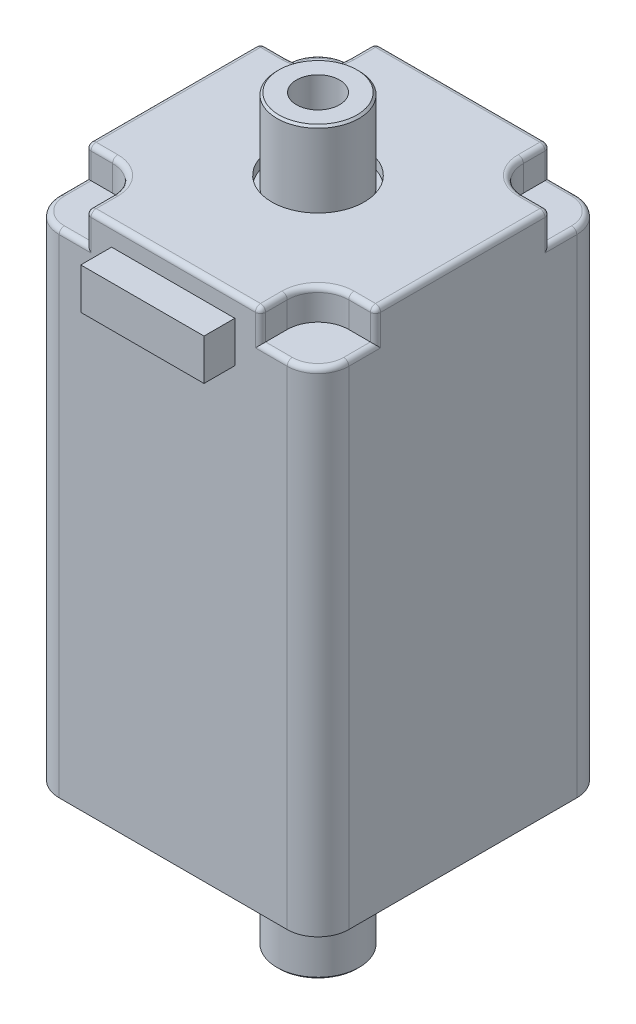
SolidWorks part; units mm, degrees
ref_plane "Front" through (0, 0, 0) normal (0, 0, 1) x (1, 0, 0)
ref_plane "Top" through (0, 0, 0) normal (0, 1, 0) x (1, 0, 0)
ref_plane "Right" through (0, 0, 0) normal (1, 0, 0) x (0, 0, -1)
sketch "Sketch1" plane through (0, 0, 0) normal (0, 1, 0) x (1, 0, 0)
  line L1 (-14.1, -14.1) -> (14.1, -14.1)
  line L2 (-14.1, -14.1) -> (-14.1, 14.1)
  line L3 (-14.1, 14.1) -> (14.1, 14.1)
  line L4 (14.1, -14.1) -> (14.1, 14.1)
  line L5 (-14.1, -14.1) -> (14.1, 14.1) construction
  line L6 (-14.1, 14.1) -> (14.1, -14.1) construction
  point P0 (0, 0)
  dimension "D1" = 28.2
extrude "Boss-Extrude1" add sketch "Sketch1" along normal blind 51
sketch "Sketch2" plane through (0, 0, 0) normal (0, -1, 0) x (1, 0, 0)
  circle A0 centre (0, 0) radius 11
  dimension "D1" = 22
extrude "Boss-Extrude2" add sketch "Sketch2" along normal blind 2
sketch "Sketch3" plane through (0, 0, 0) normal (0, -1, 0) x (1, 0, 0)
  line L0 (0, 14.1) -> (0, -14.1) construction
  line L1 (-14.1, 14.1) -> (14.1, 14.1) construction
  line L2 (14.1, -14.1) -> (-14.1, -14.1) construction
  line L3 (14.1, 0) -> (-14.1, 0) construction
  line L4 (14.1, 14.1) -> (14.1, -14.1) construction
  line L5 (-14.1, -14.1) -> (-14.1, 14.1) construction
  circle A0 centre (-11.5, 11.5) radius 0.9812
  circle A1 centre (11.5, 11.5) radius 0.9812
  circle A2 centre (11.5, -11.5) radius 0.9812
  circle A3 centre (-11.5, -11.5) radius 0.9812
  dimension "D1" = 23
  dimension "D2" = 23
hole_wizard "M2.5 Tapped Hole1" positions "Sketch5" profile "Sketch4" tap size "M2.5" standard "ISO"
sketch "Sketch5" plane through (0, 0, 0) normal (0, -1, 0) x (-1, 0, 0)
  point P1 (11.5, -11.5)
  point P4 (-11.5, -11.5)
  point P7 (-11.5, 11.5)
  point P10 (11.5, 11.5)
cosmetic thread "Hole Thread1" parameters "D1"=10, "D2"=2.5
sketch "Sketch4" plane through (-11.5, 0, 11.5) normal (1, 0, 0) x (0, 0, -1)
  line L0 (0, 0) -> (0, 15.6159)
  line L1 (0, 15.6159) -> (1.025, 15)
  line L2 (1.025, 15) -> (1.025, 0)
  line L5 (1.025, 0) -> (0, 0)
  line L10 (0, 15.6159) -> (-1.025, 15) construction
  line L11 (0, -6.35) -> (0, 107.95) construction
  dimension "Tap Drill Dia." = 2.05
  dimension "Tap Drill Depth" = 15
  dimension "Drill Angle" = 118
cosmetic thread "Hole Thread2" parameters "D1"=10, "D2"=2.5
cosmetic thread "Hole Thread3" parameters "D1"=10, "D2"=2.5
cosmetic thread "Hole Thread4" parameters "D1"=10, "D2"=2.5
fillet "Fillet1" radius 3 4 edges at (-14.1, 25.5, -14.1) (14.1, 25.5, -14.1) (14.1, 25.5, 14.1) (-14.1, 25.5, 14.1)
sketch "Sketch6" plane through (0, 0, 0) normal (0, -1, 0) x (1, 0, 0)
  circle A0 centre (0, 0) radius 4
  dimension "D1" = 8
extrude "Boss-Extrude3" add sketch "Sketch6" along normal blind 14
cosmetic thread "Cosmetic Thread1" parameters "D1"=10, "D2"=6.619
sketch "Sketch7" plane through (0, 51, 0) normal (0, 1, 0) x (1, 0, 0)
  circle A0 centre (0, 0) radius 4
  dimension "D1" = 8
extrude "Boss-Extrude4" add sketch "Sketch7" along normal blind 7
hole_wizard "M5 Tapped Hole1" positions "Sketch9" profile "Sketch8" tap size "M5" standard "ISO" end condition through all
sketch "Sketch9" plane through (0, 58, 0) normal (0, 1, 0) x (1, 0, 0)
  point P0 (0, 0)
sketch "Sketch8" plane through (0, 58, 0) normal (1, 0, 0) x (0, 0, 1)
  line L0 (0, 0) -> (0, 72)
  line L1 (0, 72) -> (2.1, 72)
  line L2 (2.1, 72) -> (2.1, 0)
  line L5 (2.1, 0) -> (0, 0)
  line L11 (0, -6.35) -> (0, 107.95) construction
  dimension "Thru Tap Drill Dia." = 4.2
  dimension "Thru Tap Drill Depth" = 72
cosmetic thread "Hole Thread5" parameters "D1"=6, "D2"=5
chamfer "Chamfer1" distance 0.2 angle 45 1 edges at (0, -2, -11)
sketch "Sketch10" plane through (0, 51, 0) normal (0, 1, 0) x (1, 0, 0)
  circle A0 centre (0, 0) radius 4
  circle A1 centre (0, 0) radius 4.5
  circle A2 centre (0, 0) radius 4 construction
  dimension "D1" = 0.5
extrude "Cut-Extrude1" cut sketch "Sketch10" against normal blind 1
sketch "Sketch11" plane through (0, 0, 14.1) normal (0, 0, 1) x (1, 0, 0)
  line L0 (0, 51) -> (0, 0) construction
  line L1 (-11.1, 51) -> (11.1, 51) construction
  line L3 (6, 45) -> (-6, 45)
  line L4 (6, 45) -> (6, 49)
  line L5 (6, 49) -> (-6, 49)
  line L6 (-6, 45) -> (-6, 49)
  line L7 (6, 45) -> (-6, 49) construction
  line L8 (6, 49) -> (-6, 45) construction
  point P5 (0, 47)
  dimension "D1" = 12
  dimension "D2" = 4
  dimension "D3" = 2
extrude "Boss-Extrude5" add sketch "Sketch11" along normal blind 3
sketch "Sketch12" plane through (0, 51, 0) normal (0, 1, 0) x (1, 0, 0)
  line L0 (0, 14.1) -> (0, 0) construction
  line L1 (11.1, 14.1) -> (-11.1, 14.1) construction
  line L2 (0, 0) -> (-14.1, 0) construction
  line L3 (-14.1, 11.1) -> (-14.1, -11.1) construction
  line L4 (-8.5, 11.5) -> (-8.5, 14.1)
  line L5 (-11.5, 8.5) -> (-14.1, 8.5)
  line L6 (-8.5, 14.1) -> (-14.1, 14.1)
  line L7 (-14.1, 14.1) -> (-14.1, 8.5)
  circle A0 centre (-11.5, 11.5) radius 3 construction
  arc A1 (-8.5, 11.5) -> (-11.5, 8.5) centre (-11.5, 11.5) cw
  line M5 (11.1, 14.1) -> (-11.1, 14.1)
  arc M6 (-11.1, 14.1) -> (-14.1, 11.1) centre (-11.1, 11.1) ccw
  line M7 (-14.1, 11.1) -> (-14.1, -11.1)
  dimension "D3" = 6
  dimension "D1" = 23
  dimension "D2" = 23
extrude "Cut-Extrude2" cut sketch "Sketch12" against normal blind 3 contours A1 L4 L5 M5 M6 M7
pattern_circular "CirPattern1" count 4 every 90 about axis through (0, 0, 0) along (0, 1, 0) of "Cut-Extrude2"
fillet "Fillet2" radius 0.5 36 edges at (14.1, 48, -9.8) (9.8, 48, -14.1) (9.8, 48, 14.1) (13.2213, 48, 13.2213) (-9.8, 48, -14.1) (-14.1, 48, -9.8) (-14.1, 48, 9.8) (-8.5, 51, -12.8) (-12.8, 51, -8.5) (12.8, 51, -8.5) (8.5, 51, -12.8) (8.5, 51, 12.8) (12.8, 51, 8.5) (-12.8, 51, 8.5) (-8.5, 51, 12.8) (13.2213, 48, -13.2213) (8.5, 49.5, -14.1) (14.1, 49.5, -8.5) (8.5, 49.5, 14.1) (14.1, 49.5, 8.5) (14.1, 48, 9.8) (-13.2213, 48, -13.2213) (-13.2213, 48, 13.2213) (-9.8, 48, 14.1) (-8.5, 49.5, 14.1) (-14.1, 49.5, 8.5) (-14.1, 49.5, -8.5) (-8.5, 49.5, -14.1) (-9.3787, 51, -9.3787) (0, 51, -14.1) (14.1, 51, 0) (9.3787, 51, -9.3787) (9.3787, 51, 9.3787) (0, 51, 14.1) (-9.3787, 51, 9.3787) (-14.1, 51, 0)
